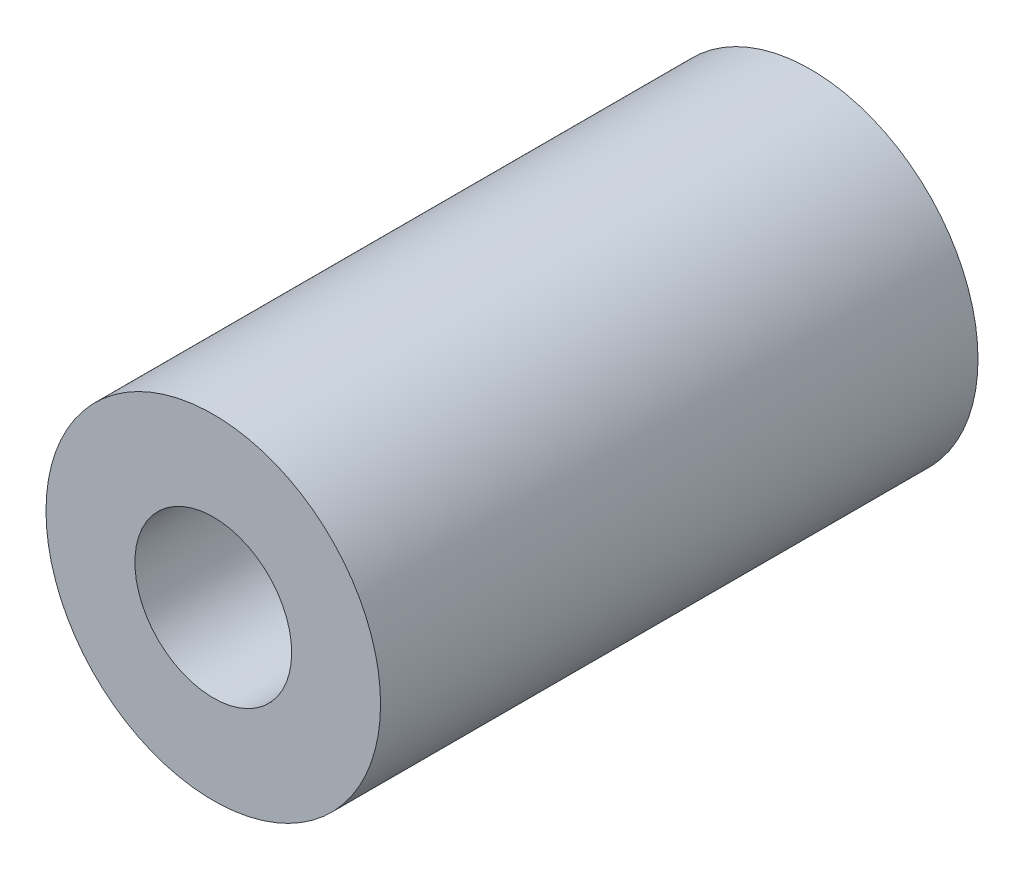
SolidWorks part; units mm, degrees
ref_plane "Front Plane" through (0, 0, 0) normal (0, 0, 1) x (1, 0, 0)
ref_plane "Top Plane" through (0, 0, 0) normal (0, 1, 0) x (1, 0, 0)
ref_plane "Right Plane" through (0, 0, 0) normal (1, 0, 0) x (0, 0, -1)
sketch "Sketch1" plane through (0, 0, 0) normal (0, 0, 1) x (1, 0, 0)
  circle A0 centre (0, 0) radius 5.334
  circle A1 centre (0, 0) radius 2.3813
  dimension "D1" = 10.668
  dimension "D2" = 4.7625
extrude "Boss-Extrude1" add sketch "Sketch1" along normal blind 19.05
sketch "Sketch2" plane through (0, 0, 19.05) normal (0, 0, 1) x (1, 0, 0)
  circle A0 centre (0, 0) radius 2.5
  circle A1 centre (0, 0) radius 5.334 construction
  dimension "D1" = 5
extrude "Cut-Extrude1" cut sketch "Sketch2" against normal mid plane 19.05
